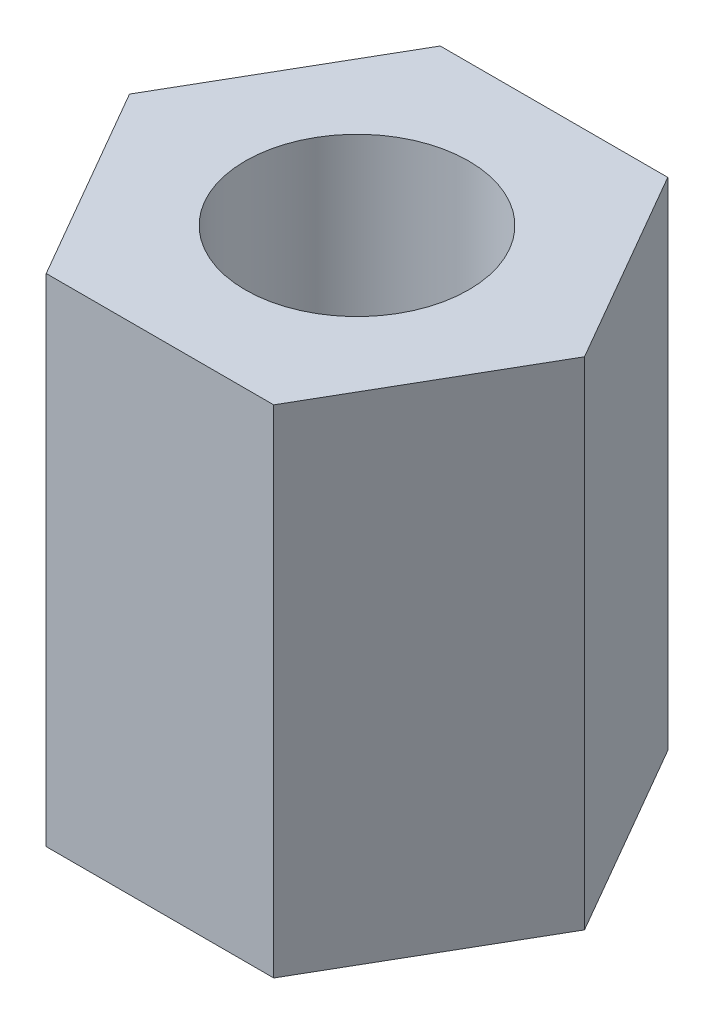
SolidWorks part; units mm, degrees
ref_plane "Front Plane" through (0, 0, 0) normal (0, 0, 1) x (1, 0, 0)
ref_plane "Top Plane" through (0, 0, 0) normal (0, 1, 0) x (1, 0, 0)
ref_plane "Right Plane" through (0, 0, 0) normal (1, 0, 0) x (0, 0, -1)
sketch "Sketch2" plane through (0, 0, 0) normal (0, 1, 0) x (1, 0, 0)
  line L1 (2.75, 0) -> (1.375, 2.3816)
  line L2 (1.375, 2.3816) -> (-1.375, 2.3816)
  line L3 (-1.375, 2.3816) -> (-2.75, 0)
  line L4 (-2.75, 0) -> (-1.375, -2.3816)
  line L5 (-1.375, -2.3816) -> (1.375, -2.3816)
  line L6 (1.375, -2.3816) -> (2.75, 0)
  circle A0 centre (0, 0) radius 2.75 construction
  circle A1 centre (0, 0) radius 1.35
  dimension "D2" = 2.7
  dimension "D1" = 5.5
extrude "Boss-Extrude1" add sketch "Sketch2" along normal blind 6
